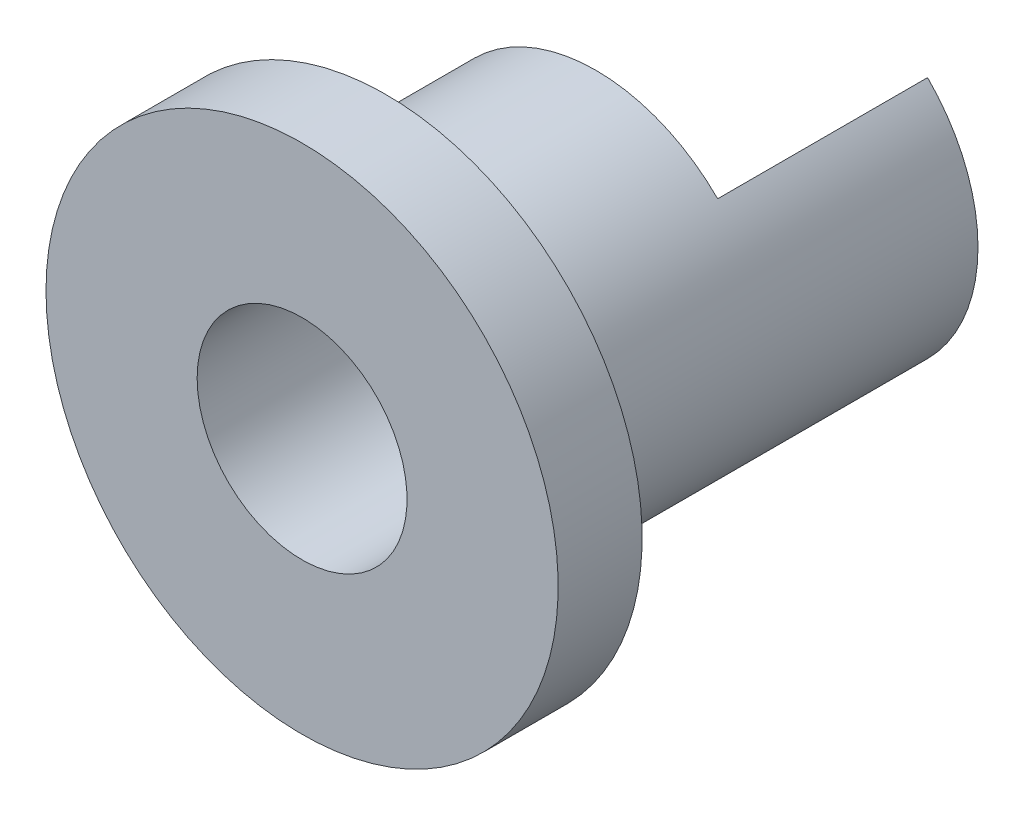
SolidWorks part; units mm, degrees
ref_plane "Plan de face" through (0, 0, 0) normal (0, 0, 1) x (1, 0, 0)
ref_plane "Plan de dessus" through (0, 0, 0) normal (0, 1, 0) x (1, 0, 0)
ref_plane "Plan de droite" through (0, 0, 0) normal (1, 0, 0) x (0, 0, -1)
sketch "Esquisse1" plane through (0, 0, 0) normal (0, 1, 0) x (1, 0, 0)
  line L0 (0, 7.5974) -> (0, -7.7532) construction
  line L1 (-2.5, 0) -> (-6.1, 0)
  line L2 (-6.1, 0) -> (-6.1, 2)
  line L3 (-6.1, 2) -> (-4.1, 2)
  line L4 (-4.1, 2) -> (-4.1, 7)
  line L5 (-4.1, 7) -> (-2.5, 7)
  line L6 (-2.5, 7) -> (-2.5, 0)
  dimension "D1" = 2.5
  dimension "D2" = 4.1
  dimension "D3" = 2
  dimension "D4" = 2
  dimension "D5" = 5
revolve "Révolution1" add sketch "Esquisse1" angle 360 about L0
sketch "Esquisse2" plane through (0, 0, -7) normal (0, 0, -1) x (-1, 0, 0)
  line L0 (0, 0) -> (-8.1667, 0) construction
  line L1 (0, 0) -> (-5.2206, 5.2206) construction
  line L2 (0, 0) -> (-5.3419, -5.3419) construction
  line L3 (-2.8991, 2.8991) -> (-1.7678, 1.7678)
  line L4 (-1.7678, -1.7678) -> (-2.8991, -2.8991)
  arc A0 (-1.7678, 1.7678) -> (-1.7678, -1.7678) centre (0, 0) ccw
  arc A1 (-2.8991, 2.8991) -> (-2.8991, -2.8991) centre (0, 0) ccw
  circle A2 centre (0, 0) radius 2.5 construction
  circle A3 centre (0, 0) radius 4.1 construction
  point P15 (0, 0)
  point P16 (0, 0)
  point P17 (0, 0)
  point P18 (0, 0)
  dimension "D1" = 45
  dimension "D2" = 45
extrude "Boss.-Extru.1" add sketch "Esquisse2" along normal blind 5
